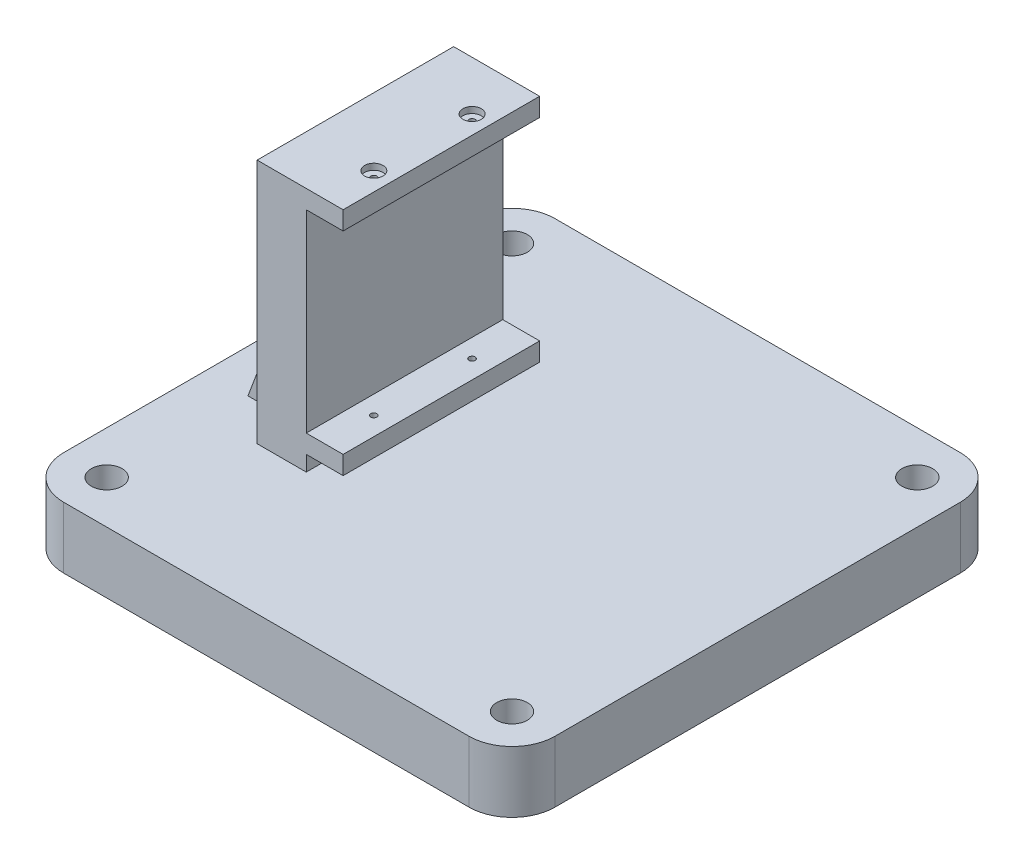
SolidWorks part; units mm, degrees
material "Custom Plastic"
ref_plane "Front Plane" through (0, 0, 0) normal (0, 0, 1) x (1, 0, 0)
ref_plane "Top Plane" through (0, 0, 0) normal (0, 1, 0) x (1, 0, 0)
ref_plane "Right Plane" through (0, 0, 0) normal (1, 0, 0) x (0, 0, -1)
sketch "Sketch1" plane through (0, 0, 0) normal (0, 1, 0) x (1, 0, 0)
  line L0 (0, 0) -> (98.4695, 0) construction
  line L1 (-33, -40) -> (33, -40)
  line L2 (-40, -33) -> (-40, 33)
  line L3 (-33, 40) -> (33, 40)
  line L4 (40, -33) -> (40, 33)
  line L5 (0, 0) -> (0, -72.4617) construction
  circle A2 centre (33, -33) radius 2.5
  arc A5 (33, -40) -> (40, -33) centre (33, -33) ccw
  arc A6 (-33, -40) -> (-40, -33) centre (-33, -33) cw
  circle A7 centre (-33, -33) radius 2.5
  arc A8 (33, 40) -> (40, 33) centre (33, 33) cw
  circle A9 centre (33, 33) radius 2.5
  arc A10 (-33, 40) -> (-40, 33) centre (-33, 33) ccw
  circle A11 centre (-33, 33) radius 2.5
  point P0 (0, 0)
  dimension "D5" = 5
  dimension "D1" = 33
  dimension "D2" = 33
extrude "Boss-Extrude1" add sketch "Sketch1" along normal blind 10
sketch "Sketch2" plane through (0, 10, 0) normal (0, 1, 0) x (1, 0, 0)
  point P0 (0, 0)
sketch "Sketch5" plane through (0, 10, 0) normal (0, 1, 0) x (1, 0, 0)
  line L0 (0, 0) -> (11.8386, 0) construction
  line L1 (-25.5, -16) -> (-17.5, -16)
  line L2 (-25.5, -16) -> (-25.5, 16)
  line L3 (-25.5, 16) -> (-17.5, 16)
  line L4 (-17.5, -16) -> (-17.5, 16)
  line L5 (-25.5, -16) -> (-17.5, 16) construction
  line L6 (-25.5, 16) -> (-17.5, -16) construction
  point P0 (-21.5, 0)
  dimension "D1" = 32
  dimension "D2" = 17.5
  dimension "D3" = 8
extrude "Boss-Extrude4" add sketch "Sketch5" along normal blind 40 contours L2 L1 L4 L3
sketch "Sketch6" plane through (0, 0, 0) normal (0, 0, 1) x (1, 0, 0)
  line L0 (-33, 10) -> (-25.5, 30)
  line L1 (-25.5, 50) -> (-25.5, 10) construction
  line L2 (-25.5, 30) -> (-25.5, 10)
  line L3 (-25.5, 10) -> (-33, 10)
extrude "Boss-Extrude5" add sketch "Sketch6" along normal mid plane 20
sketch "Sketch7" plane through (-17.5, 0, 0) normal (1, 0, 0) x (0, 0, -1)
  line L0 (16, 50) -> (16, 10) construction
  line L1 (-16, 50) -> (16, 50)
  line L2 (-16, 50) -> (-16, 47)
  line L3 (-16, 47) -> (16, 47)
  line L4 (16, 50) -> (16, 47)
  line L5 (-16, 50) -> (-16, 10) construction
  line L6 (-16, 15.5) -> (16, 15.5)
  line L7 (-16, 15.5) -> (-16, 12.5)
  line L8 (-16, 12.5) -> (16, 12.5)
  line L9 (16, 15.5) -> (16, 12.5)
  dimension "D1" = 3
  dimension "D2" = 31.5
  dimension "D3" = 3
extrude "Boss-Extrude6" add sketch "Sketch7" along normal blind 6
sketch "Sketch8" plane through (0, 50, 0) normal (0, 1, 0) x (1, 0, 0)
  line L0 (-11.5, 16) -> (-11.5, -16) construction
  line L1 (0, 0) -> (-36.6736, 0) construction
  circle A0 centre (-14.5, -8) radius 0.5
  circle A1 centre (-14.5, 8) radius 0.5
  point P9 (0, 0)
  point P10 (-14.5, 11.1339)
  dimension "D1" = 1
  dimension "D2" = 1
  dimension "D3" = 3
  dimension "D4" = 3
  dimension "D5" = 16
  dimension "D6" = 8
extrude "Cut-Extrude1" cut sketch "Sketch8" against normal blind 39
sketch "Sketch9" plane through (0, 50, 0) normal (0, 1, 0) x (1, 0, 0)
  circle A0 centre (-14.5, 8) radius 1.5
  circle A1 centre (-14.5, -8) radius 1.5
  dimension "D1" = 3
extrude "Cut-Extrude2" cut sketch "Sketch9" against normal blind 1
